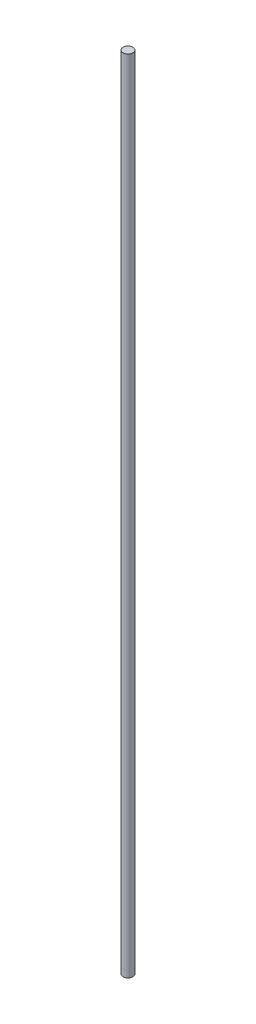
SolidWorks part; units mm, degrees
ref_plane "Front Plane" through (0, 0, 0) normal (0, 0, 1) x (1, 0, 0)
ref_plane "Top Plane" through (0, 0, 0) normal (0, 1, 0) x (1, 0, 0)
ref_plane "Right Plane" through (0, 0, 0) normal (1, 0, 0) x (0, 0, -1)
sketch "Croquis1" plane through (0, 0, 0) normal (0, 1, 0) x (1, 0, 0)
  circle A0 centre (0, 0) radius 4
  dimension "D1" = 8
extrude "Saliente-Extruir1" add sketch "Croquis1" along normal blind 650
